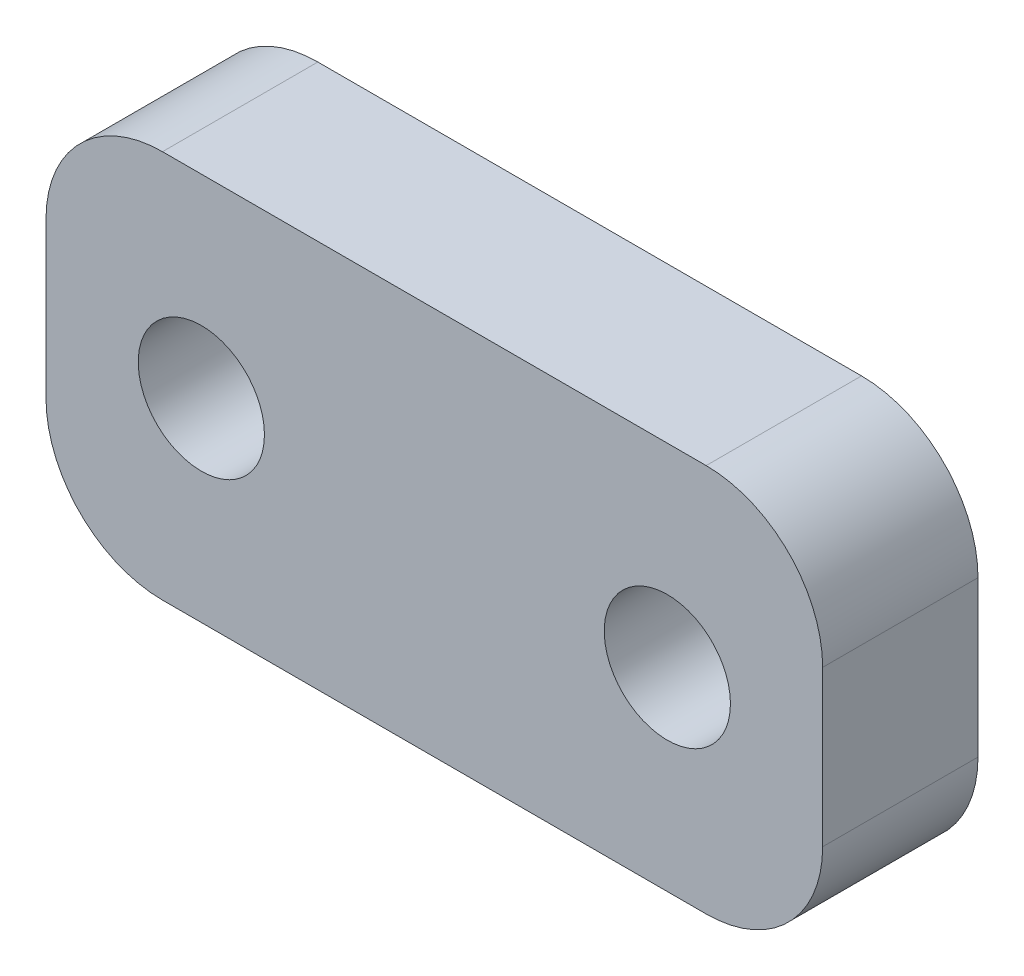
SolidWorks part; units mm, degrees
ref_plane "Alzado" through (0, 0, 0) normal (0, 0, 1) x (1, 0, 0)
ref_plane "Planta" through (0, 0, 0) normal (0, 1, 0) x (1, 0, 0)
ref_plane "Vista lateral" through (0, 0, 0) normal (1, 0, 0) x (0, 0, -1)
sketch "Croquis1" plane through (0, 0, 0) normal (0, 0, 1) x (1, 0, 0)
  line L0 (-6, 0) -> (6, 0) construction
  line L1 (-10, -5.0002) -> (10, -5.0002)
  line L2 (-10, -5.0002) -> (-10, 5.0002)
  line L3 (-10, 5.0002) -> (10, 5.0002)
  line L4 (10, -5.0002) -> (10, 5.0002)
  line L5 (-10, -5.0002) -> (10, 5.0002) construction
  line L6 (-10, 5.0002) -> (10, -5.0002) construction
  circle A0 centre (-6, 0) radius 1.625
  circle A1 centre (6, 0) radius 1.625
  point P0 (0, 0)
  dimension "D3" = 3.25
  dimension "D1" = 20
  dimension "D2" = 10.0003
  dimension "D4" = 12
extrude "Saliente-Extruir1" add sketch "Croquis1" along normal blind 4
fillet "Redondeo1" radius 3 4 edges at (10, 5.0002, 2) (10, -5.0002, 2) (-10, -5.0002, 2) (-10, 5.0002, 2)
move or copy body "Sólido-Mover/Copiar1" [suppressed] bodies to move or copy 101
